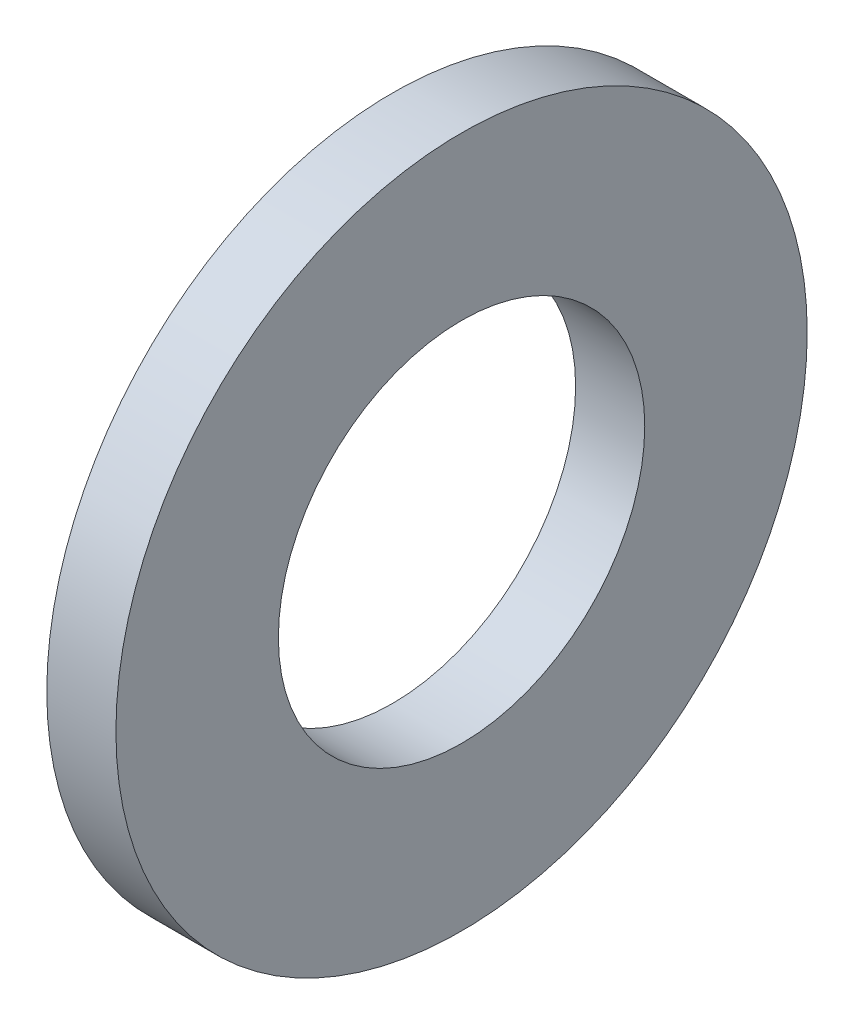
SolidWorks part; units mm, degrees
ref_plane "Plane1" through (0, 0, 0) normal (0, 0, 1) x (1, 0, 0)
ref_plane "Plane2" through (0, 0, 0) normal (0, 1, 0) x (1, 0, 0)
ref_plane "Plane3" through (0, 0, 0) normal (1, 0, 0) x (0, 0, -1)
sketch "Sketch1" plane through (0, 0, 0) normal (0, 0, 1) x (1, 0, 0)
  line L0 (-34.925, 0) -> (9.525, 0) construction
  line L1 (0, 2.65) -> (0, 5)
  line L2 (0, 5) -> (-1, 5)
  line L3 (-1, 5) -> (-1, 2.65)
  line L4 (-1, 2.65) -> (0, 2.65)
  dimension "Thickness" = 1
  dimension "Inside_dia" = 5.3
  dimension "Outside_dia" = 10
revolve "Base-Revolve" add sketch "Sketch1" angle 360 about L0
